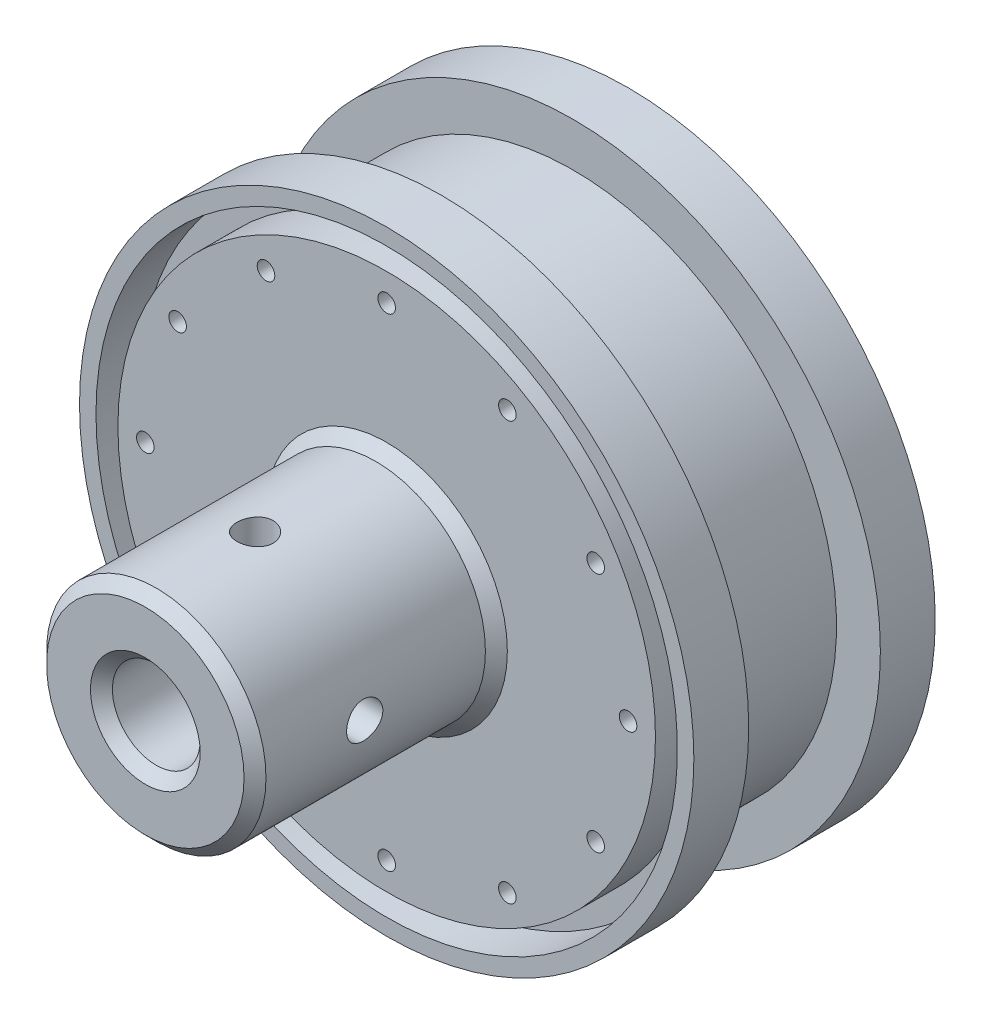
SolidWorks part; units mm, degrees
material "1060 Alloy"
ref_plane "Front Plane" through (0, 0, 0) normal (0, 0, 1) x (1, 0, 0)
ref_plane "Top Plane" through (0, 0, 0) normal (0, 1, 0) x (1, 0, 0)
ref_plane "Right Plane" through (0, 0, 0) normal (1, 0, 0) x (0, 0, -1)
sketch "Sketch1" plane through (0, 0, 0) normal (0, 0, 1) x (1, 0, 0)
  circle A0 centre (0, 0) radius 28
  dimension "D1" = 56
extrude "Boss-Extrude1" add sketch "Sketch1" along normal blind 22
sketch "Sketch2" plane through (0, 0, 22) normal (0, 0, 1) x (1, 0, 0)
  circle A0 centre (0, 0) radius 10
  dimension "D1" = 20
extrude "Boss-Extrude2" add sketch "Sketch2" along normal blind 22
sketch "Sketch3" plane through (0, 0, 0) normal (0, 0, -1) x (-1, 0, 0)
  circle A0 centre (0, 0) radius 20
  circle A1 centre (0, 0) radius 28 construction
  dimension "D1" = 8
extrude "Cut-Extrude1" cut sketch "Sketch3" against normal blind 16
chamfer "Chamfer1" distance 4 angle 45 1 edges at (-20, 0, 16)
sketch "Sketch4" plane through (0, 0, 44) normal (0, 0, 1) x (1, 0, 0)
  circle A0 centre (0, 0) radius 4
  dimension "D1" = 8
extrude "Cut-Extrude2" cut sketch "Sketch4" against normal blind 20
hole_wizard "CBORE for M3 Hex Socket Head Cap Screw1" positions "Sketch5" profile "Sketch6" counterbore size "M3" standard "ISO" end condition through all
sketch "Sketch5" plane through (0, 0, 16) normal (0, 0, -1) x (-1, 0, 0)
  point P0 (0, 0)
sketch "Sketch6" plane through (0, 0, 16) normal (1, 0, 0) x (0, 1, 0)
  line L0 (0, 0) -> (0, 28)
  line L1 (0, 28) -> (1.7, 28)
  line L3 (1.7, 28) -> (1.7, 3.4)
  line L4 (1.7, 3.4) -> (3.25, 3.4)
  line L5 (3.25, 3.4) -> (3.25, 0)
  line L7 (3.25, 0) -> (0, 0)
  line L11 (0, -6.35) -> (0, 107.95) construction
  dimension "Thru Hole Dia." = 3.4
  dimension "Thru Hole Depth" = 28
  dimension "C'Bore Dia." = 6.5
  dimension "C'Bore Depth" = 3.4
sketch "Sketch7" plane through (0, 0, 0) normal (0, 0, -1) x (-1, 0, 0)
  circle A0 centre (0, 0) radius 26.5
  circle A1 centre (0, 0) radius 24.5
  circle A2 centre (0, 0) radius 28 construction
  dimension "D1" = 2
  dimension "D2" = 1.5
extrude "Cut-Extrude3" cut sketch "Sketch7" against normal blind 4
ref_plane "Plane1" through (0, 0, 11) normal (0, 0, -1) x (-1, 0, 0)
mirror "Mirror1" about plane through (0, 0, 11) normal (0, 0, -1) of "Cut-Extrude3"
hole_wizard "M2 Tapped Hole1" positions "Sketch8" profile "Sketch9" tap size "M2" standard "ISO"
sketch "Sketch8" plane through (0, 0, 0) normal (0, 0, -1) x (-1, 0, 0)
  point P0 (0, 22)
  point P9 (11, 19.0526)
  point P10 (19.0526, 11)
  point P11 (22, 0)
  point P12 (19.0526, -11)
  point P13 (11, -19.0526)
  point P14 (0, -22)
  point P15 (-11, -19.0526)
  point P16 (-19.0526, -11)
  point P17 (-22, 0)
  point P18 (-19.0526, 11)
  point P19 (-11, 19.0526)
  dimension "D1" = 22
  dimension "D2" = 12
cosmetic thread "Hole Thread1" parameters "D2"=2
cosmetic thread "Hole Thread2" parameters "D2"=2
cosmetic thread "Hole Thread3" parameters "D2"=2
cosmetic thread "Hole Thread4" parameters "D2"=2
cosmetic thread "Hole Thread5" parameters "D2"=2
cosmetic thread "Hole Thread6" parameters "D2"=2
cosmetic thread "Hole Thread7" parameters "D2"=2
cosmetic thread "Hole Thread8" parameters "D2"=2
cosmetic thread "Hole Thread9" parameters "D2"=2
cosmetic thread "Hole Thread10" parameters "D2"=2
cosmetic thread "Hole Thread11" parameters "D2"=2
cosmetic thread "Hole Thread12" parameters "D2"=2
sketch "Sketch9" plane through (0, 22, 0) normal (1, 0, 0) x (0, 1, 0)
  line L0 (0, 0) -> (0, 8.4807)
  line L1 (0, 8.4807) -> (0.8, 8)
  line L2 (0.8, 8) -> (0.8, 0)
  line L5 (0.8, 0) -> (0, 0)
  line L10 (0, 8.4807) -> (-0.8, 8) construction
  line L11 (0, -6.35) -> (0, 107.95) construction
  dimension "Tap Drill Dia." = 1.6
  dimension "Tap Drill Depth" = 8
  dimension "Drill Angle" = 118
sketch "Sketch10" plane through (0, 0, 11) normal (0, 0, -1) x (-1, 0, 0)
  circle A0 centre (0, 0) radius 24
  circle A1 centre (0, 0) radius 28 construction
  circle A2 centre (0, 0) radius 28
  dimension "D1" = 4
extrude "Cut-Extrude5" cut sketch "Sketch10" against normal blind 6 and the other way blind 6
mirror "Mirror2" about plane through (0, 0, 11) normal (0, 0, -1) of "M2 Tapped Hole1"
cosmetic thread "Hole Thread13" parameters "D1"=6.6, "D2"=2
cosmetic thread "Hole Thread14" parameters "D1"=6.6, "D2"=2
cosmetic thread "Hole Thread15" parameters "D1"=6.6, "D2"=2
cosmetic thread "Hole Thread16" parameters "D1"=6.6, "D2"=2
cosmetic thread "Hole Thread17" parameters "D1"=6.6, "D2"=2
cosmetic thread "Hole Thread18" parameters "D1"=6.6, "D2"=2
cosmetic thread "Hole Thread19" parameters "D1"=6.6, "D2"=2
cosmetic thread "Hole Thread20" parameters "D1"=6.6, "D2"=2
cosmetic thread "Hole Thread21" parameters "D1"=6.6, "D2"=2
cosmetic thread "Hole Thread22" parameters "D1"=6.6, "D2"=2
cosmetic thread "Hole Thread23" parameters "D1"=6.6, "D2"=2
cosmetic thread "Hole Thread24" parameters "D1"=6.6, "D2"=2
chamfer "Chamfer2" distance 1 angle 45 3 edges at (10, 0, 22) (10, 0, 44) (4, 0, 44)
hole_wizard "M4 Tapped Hole1" positions "3DSketch1" profile "Sketch11" tap size "M4" standard "ISO"
sketch3d "3DSketch1"
  line L0 (0, 0, 0) -> (0, 0, 50000) construction
  point P0 (0, 10, 34)
  point P9 (2.7303, 9.62, 35.1266)
  point P10 (0, 0, 0)
  point P11 (3.4187, 9.3975, 34)
  point P12 (0, 0, 0)
  point P13 (-0.0114, 10, 34)
  dimension "D1" = 10
sketch "Sketch11" plane through (0, 10, 34) normal (1, 0, 0) x (0, 0, 1)
  line L0 (0, 0) -> (0, 20)
  line L1 (0, 20) -> (1.65, 20)
  line L2 (1.65, 20) -> (1.65, 0)
  line L5 (1.65, 0) -> (0, 0)
  line L11 (0, -6.35) -> (0, 107.95) construction
  dimension "Thru Tap Drill Dia." = 3.3
  dimension "Thru Tap Drill Depth" = 20
cosmetic thread "Hole Thread25" parameters "D2"=4
pattern_circular "CirPattern1" count 2 every 90 about axis through (0, 0, 24) along (0, 0, 1) of "M4 Tapped Hole1"
cosmetic thread "Hole Thread26" parameters "D2"=4
